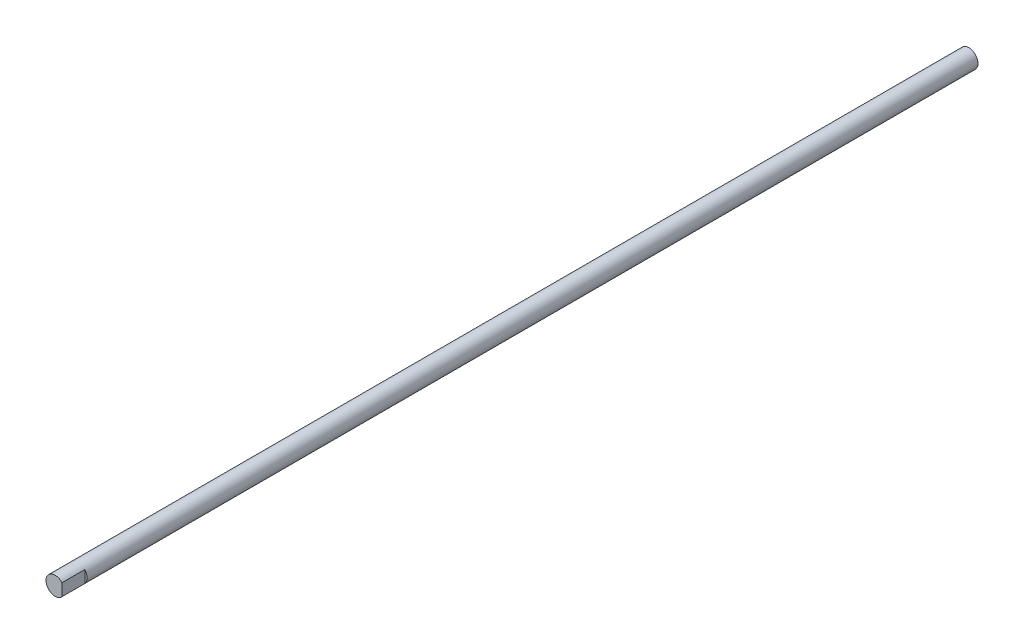
SolidWorks part; units mm, degrees
ref_plane "Alzado" through (0, 0, 0) normal (0, 0, 1) x (1, 0, 0)
ref_plane "Planta" through (0, 0, 0) normal (0, 1, 0) x (1, 0, 0)
ref_plane "Vista lateral" through (0, 0, 0) normal (1, 0, 0) x (0, 0, -1)
sketch "Croquis1" plane through (0, 0, 0) normal (0, 0, 1) x (1, 0, 0)
  circle A0 centre (0, 0) radius 4
  dimension "D1" = 8
extrude "Saliente-Extruir1" add sketch "Croquis1" along normal blind 400
sketch "Croquis4" plane through (0, 0, 400) normal (0, 0, 1) x (1, 0, 0)
  line L1 (-4, 4) -> (4, 4) construction
  line L2 (-4, 4) -> (-4, -4) construction
  line L3 (-4, -4) -> (4, -4) construction
  line L4 (4, 4) -> (4, -4) construction
  line L5 (4, 4) -> (3, 4)
  line L6 (4, 4) -> (4, -4)
  line L7 (4, -4) -> (3, -4)
  line L8 (3, 4) -> (3, -4)
  circle A0 centre (0, 0) radius 4 construction
  dimension "D1" = 7
extrude "Cortar-Extruir1" cut sketch "Croquis4" against normal blind 10
